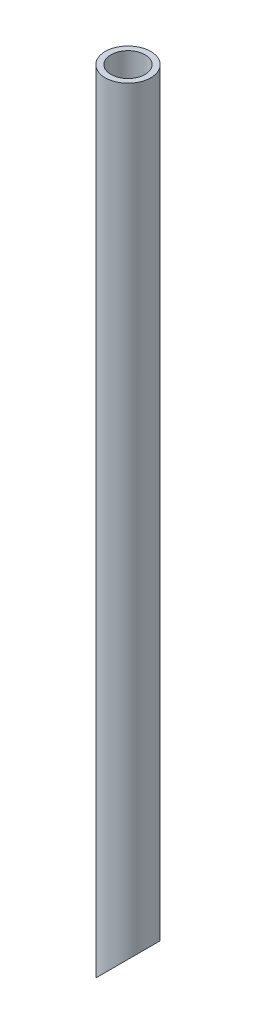
SolidWorks part; units mm, degrees
ref_plane "Спереди" through (0, 0, 0) normal (0, 0, 1) x (1, 0, 0)
ref_plane "Сверху" through (0, 0, 0) normal (0, 1, 0) x (1, 0, 0)
ref_plane "Справа" through (0, 0, 0) normal (1, 0, 0) x (0, 0, -1)
sketch "Эскиз1" plane through (0, 0, 0) normal (0, 1, 0) x (1, 0, 0)
  circle A0 centre (0, 0) radius 2
  circle A1 centre (0, 0) radius 1.5
  dimension "D1" = 4
  dimension "D2" = 0.5
extrude "Бобышка-Вытянуть1" add sketch "Эскиз1" along normal blind 70
sketch "Эскиз2" plane through (0, 0, 0) normal (0, 0, 1) x (1, 0, 0)
  line L0 (-2, 0) -> (2.9565, 4.9565)
  line L1 (-2, 0) -> (2, 0) construction
  line L2 (2.9565, 4.9565) -> (2.9565, -0.4267)
  line L3 (2.9565, -0.4267) -> (-2, -0.4267)
  line L4 (-2, -0.4267) -> (-2, 0)
  dimension "D1" = 45
extrude "Вырез-Вытянуть1" cut sketch "Эскиз2" against normal through all both and the other way through all
